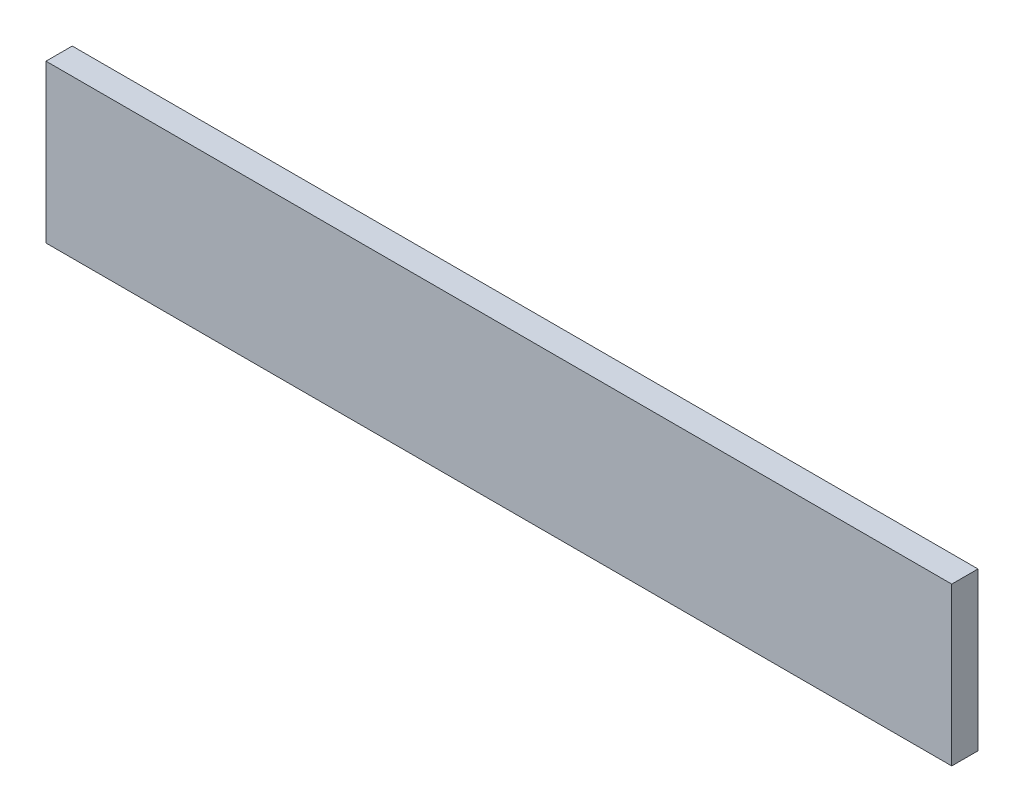
SolidWorks part; units mm, degrees
ref_plane "Front Plane" through (0, 0, 0) normal (0, 0, 1) x (1, 0, 0)
ref_plane "Top Plane" through (0, 0, 0) normal (0, 1, 0) x (1, 0, 0)
ref_plane "Right Plane" through (0, 0, 0) normal (1, 0, 0) x (0, 0, -1)
sketch "Sketch1" plane through (0, 0, 0) normal (0, 0, 1) x (1, 0, 0)
  line L1 (0, 0) -> (690, 0)
  line L2 (0, 0) -> (0, 120)
  line L3 (0, 120) -> (690, 120)
  line L4 (690, 0) -> (690, 120)
  dimension "D1" = 690
  dimension "D2" = 120
extrude "Boss-Extrude1" add sketch "Sketch1" along normal blind 20
